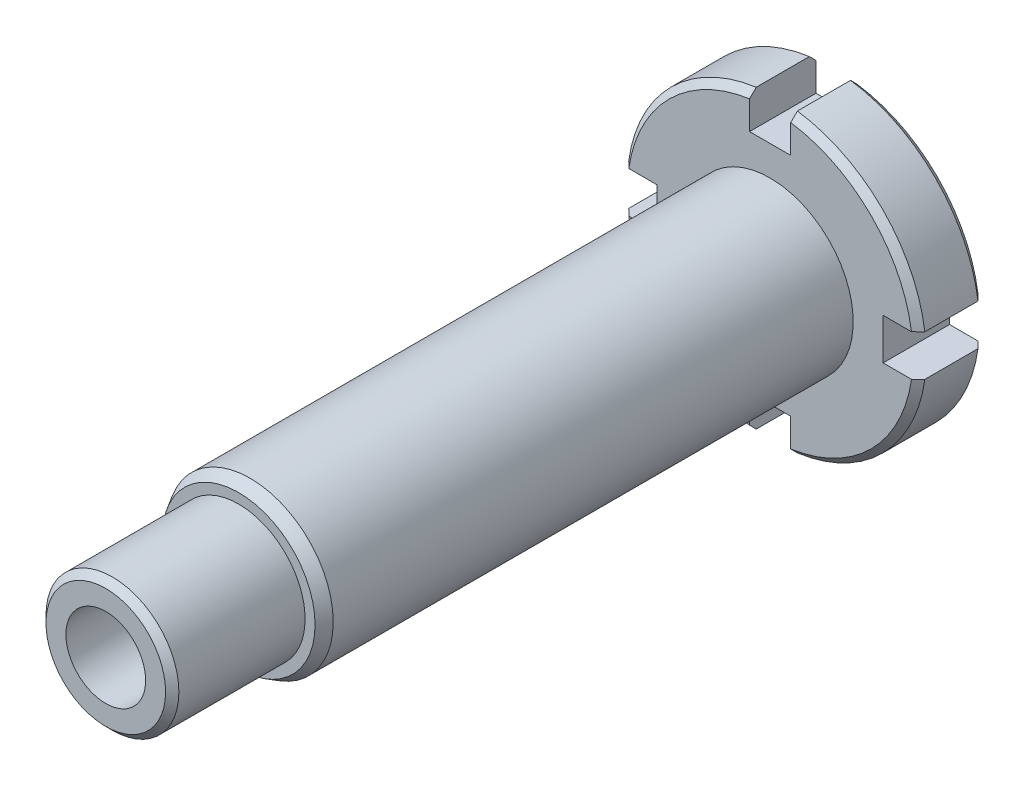
SolidWorks part; units mm, degrees
ref_plane "Plan de face" through (0, 0, 0) normal (0, 0, 1) x (1, 0, 0)
ref_plane "Plan de dessus" through (0, 0, 0) normal (0, 1, 0) x (1, 0, 0)
ref_plane "Plan de droite" through (0, 0, 0) normal (1, 0, 0) x (0, 0, -1)
sketch "Esquisse1" plane through (0, 0, 0) normal (1, 0, 0) x (0, 0, -1)
  line L0 (0, 0) -> (-113.6905, 0) construction
  line L1 (-110, 0) -> (-110, 10)
  line L2 (-90, 12.5) -> (-10, 12.5)
  line L3 (-10, 12.5) -> (-10, 22.5)
  line L4 (-10, 22.5) -> (0, 22.5)
  line L5 (0, 22.5) -> (0, 0)
  line L6 (0, 0) -> (-110, 0)
  line L7 (-90, 12.5) -> (-90, 10)
  line L8 (-90, 10) -> (-110, 10)
  dimension "D1" = 10
  dimension "D2" = 12.5
  dimension "D3" = 22.5
  dimension "D4" = 80
  dimension "D5" = 20
  dimension "D6" = 10
revolve "Révolution1" add sketch "Esquisse1" angle 360 about L0
cosmetic thread "Représentation de filetage1" parameters "D1"=20, "D2"=17.252
sketch "Esquisse2" plane through (0, 0, 0) normal (0, 0, -1) x (-1, 0, 0)
  line L0 (0, 0) -> (0, 15.963) construction
  line L1 (-3.1, 22.2854) -> (-3.1, 17)
  line L2 (-3.1, 17) -> (3.1, 17)
  line L3 (3.1, 17) -> (3.1, 22.2854)
  circle A0 centre (0, 0) radius 22.5 construction
  arc A3 (3.1, 22.2854) -> (-3.1, 22.2854) centre (0, 0) ccw
  dimension "D2" = 17
  dimension "D1" = 6.2
chamfer "Chanfrein1" distance 1 angle 45 3 edges at (-10, 0, 110) (-22.5, 0, 10) (-22.5, 0, 0)
sketch "Esquisse3" plane through (0, 0, 0) normal (0, 0, -1) x (-1, 0, 0)
  circle A0 centre (0, 0) radius 6
  dimension "D1" = 12
extrude "Enlèv. mat.-Extru.2" cut sketch "Esquisse3" against normal through all
extrude "Enlèv. mat.-Extru.1" cut sketch "Esquisse2" against normal through all
pattern_circular "Répétition circulaire1" count 4 over 360 about axis through (0, 0, 0) along (0, 0, 1) of "Enlèv. mat.-Extru.1"
chamfer "Chanfrein2" distance 1 angle 60 1 edges at (-12.5, 0, 90)
